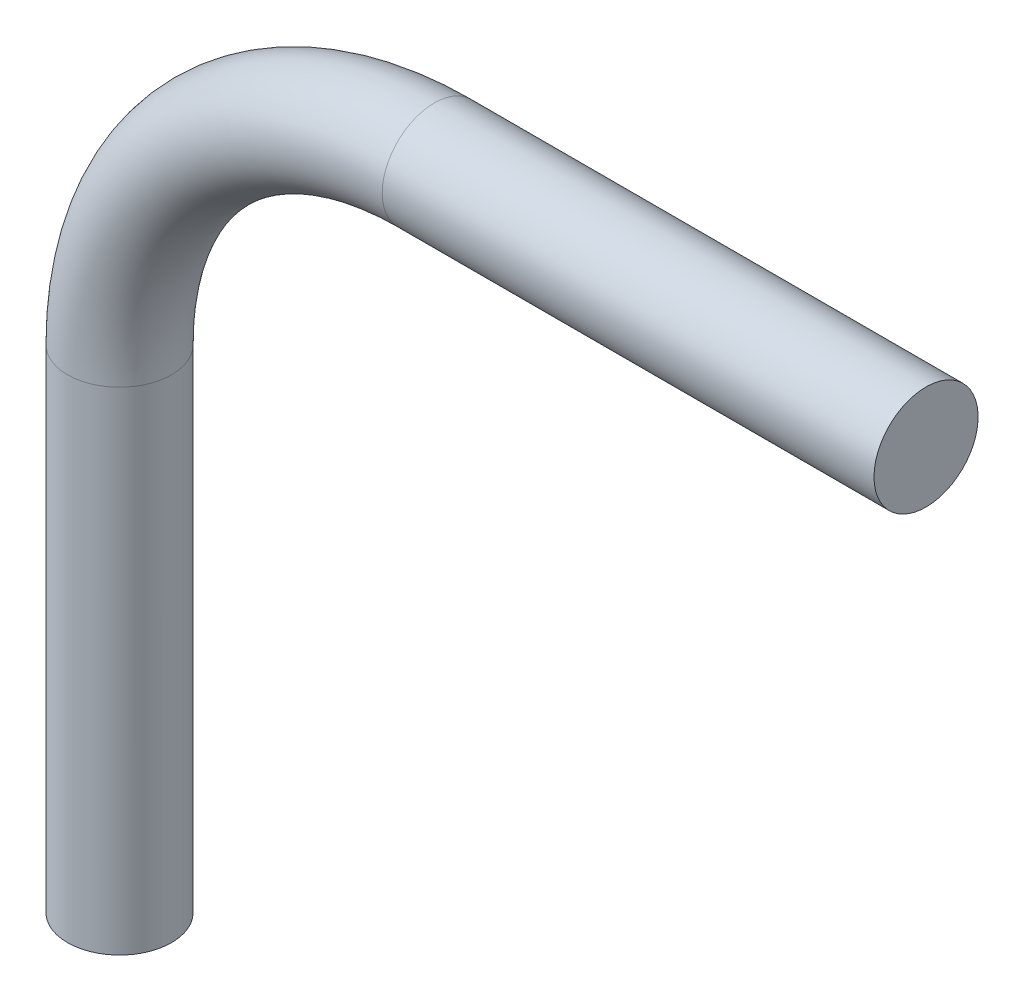
SolidWorks part; units mm, degrees
ref_plane "Plan de face" through (0, 0, 0) normal (0, 0, 1) x (1, 0, 0)
ref_plane "Plan de dessus" through (0, 0, 0) normal (0, 1, 0) x (1, 0, 0)
ref_plane "Plan de droite" through (0, 0, 0) normal (1, 0, 0) x (0, 0, -1)
sketch "Esquisse1" plane through (0, 0, 0) normal (0, 0, 1) x (1, 0, 0)
  line L0 (0, 19.2) -> (30, 19.2)
  line L1 (-19.2, 0) -> (-19.2, -30)
  arc A0 (-19.2, 0) -> (0, 19.2) centre (0, 0) cw
  point P4 (0, 0)
sweep "Balayage1" add path "Esquisse1" circular profile diameter 6.35 parameters "D3"=6.35
